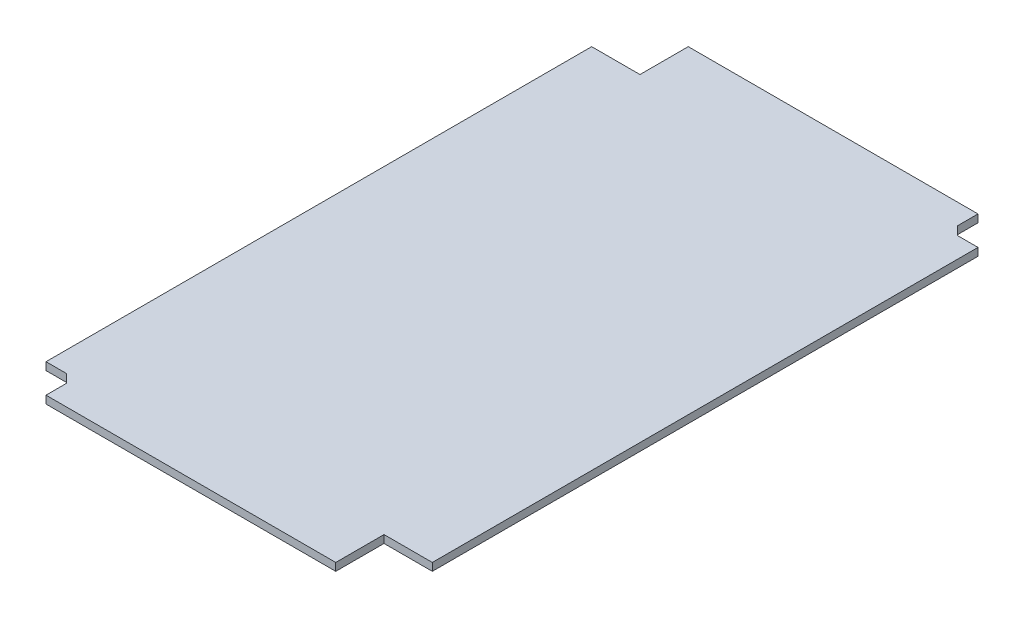
SolidWorks part; units mm, degrees
ref_plane "Front Plane" through (0, 0, 0) normal (0, 0, 1) x (1, 0, 0)
ref_plane "Top Plane" through (0, 0, 0) normal (0, 1, 0) x (1, 0, 0)
ref_plane "Right Plane" through (0, 0, 0) normal (1, 0, 0) x (0, 0, -1)
sketch "Sketch2" plane through (0, 0, 0) normal (0, 1, 0) x (1, 0, 0)
  line L0 (0, 123) -> (10, 123) construction
  line L1 (0, 0) -> (70, 0) construction
  line L2 (0, 0) -> (0, 123) construction
  line L3 (10, 133) -> (80, 133) construction
  line L4 (80, 10) -> (80, 133) construction
  line L5 (10, 123) -> (10, 133) construction
  line L6 (70, 0) -> (70, 10) construction
  line L7 (70, 10) -> (80, 10) construction
  line L8 (8, 2) -> (68, 2)
  line L9 (68, 2) -> (68, 12)
  line L10 (68, 12) -> (78, 12)
  line L11 (78, 12) -> (78, 125)
  line L12 (12, 131) -> (72, 131)
  line L13 (12, 121) -> (12, 131)
  line L14 (2, 121) -> (12, 121)
  line L15 (2, 8) -> (2, 121)
  line L16 (12, 131) -> (78, 131) construction
  line L17 (78, 12) -> (78, 131) construction
  line L18 (2, 2) -> (2, 121) construction
  line L19 (2, 2) -> (68, 2) construction
  line L20 (2, 8) -> (6.2426, 8)
  line L21 (8, 6.2426) -> (8, 2)
  line L22 (6.2426, 8) -> (8, 6.2426)
  line L23 (72, 128) -> (72, 131)
  line L24 (75, 125) -> (78, 125)
  line L25 (72, 128) -> (72, 126.7574)
  line L26 (73.7574, 125) -> (75, 125)
  line L27 (73.7574, 125) -> (72, 126.7574)
  circle A0 centre (75, 128) radius 2.5 construction
  circle A1 centre (5, 5) radius 2.5 construction
  arc A2 (8, 5) -> (5, 8) centre (5, 5) ccw construction
  arc A3 (72, 128) -> (75, 125) centre (75, 128) ccw construction
  circle A4 centre (75, 128) radius 3 construction
  circle A5 centre (5, 5) radius 3 construction
  dimension "D7" = 5
  dimension "D8" = 5
  dimension "D9" = 5
  dimension "D1" = 80
  dimension "D2" = 133
  dimension "D3" = 10
  dimension "D4" = 10
  dimension "D5" = 10
  dimension "D6" = 10
  dimension "D10" = 5
  dimension "D11" = 5
  dimension "D12" = 5
  dimension "D15" = 45
  dimension "D16" = 6
  dimension "D17" = 6
  dimension "D18" = 45
  dimension "D13" = 2
  dimension "D14" = 0.5
extrude "Boss-Extrude1" add sketch "Sketch2" along normal blind 1.6
